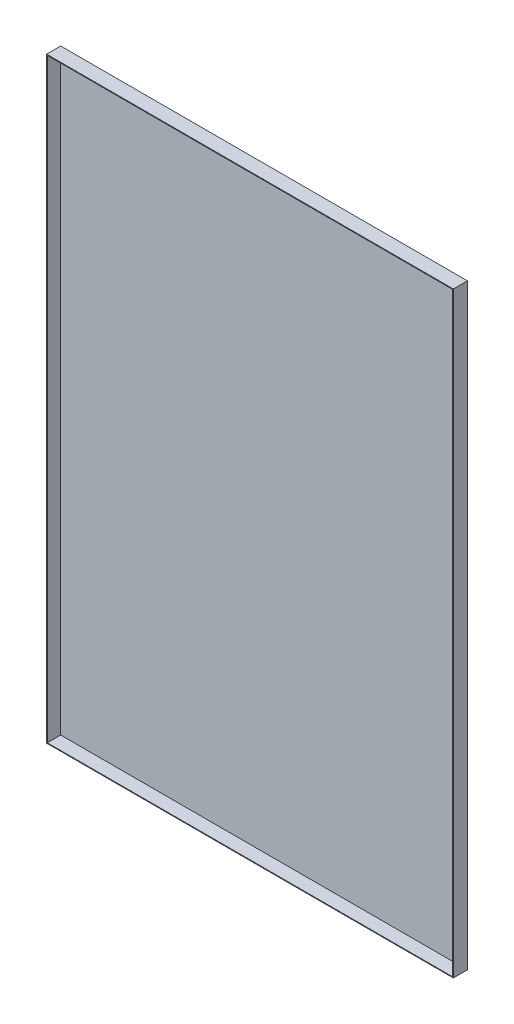
SolidWorks part; units mm, degrees
ref_plane "前视基准面" through (0, 0, 0) normal (0, 0, 1) x (1, 0, 0)
ref_plane "上视基准面" through (0, 0, 0) normal (0, 1, 0) x (1, 0, 0)
ref_plane "右视基准面" through (0, 0, 0) normal (1, 0, 0) x (0, 0, -1)
sketch "草图1" plane through (0, 0, 0) normal (0, 0, 1) x (1, 0, 0)
  line L1 (-289, 424) -> (289, 424)
  line L2 (-289, 424) -> (-289, -424)
  line L3 (-289, -424) -> (289, -424)
  line L4 (289, 424) -> (289, -424)
  line L5 (-289, 424) -> (289, -424) construction
  line L6 (-289, -424) -> (289, 424) construction
  point P0 (0, 0)
  dimension "D1" = 578
  dimension "D2" = 848
extrude "凸台-拉伸1" add sketch "草图1" along normal blind 20
shell "抽壳1" thickness 1
